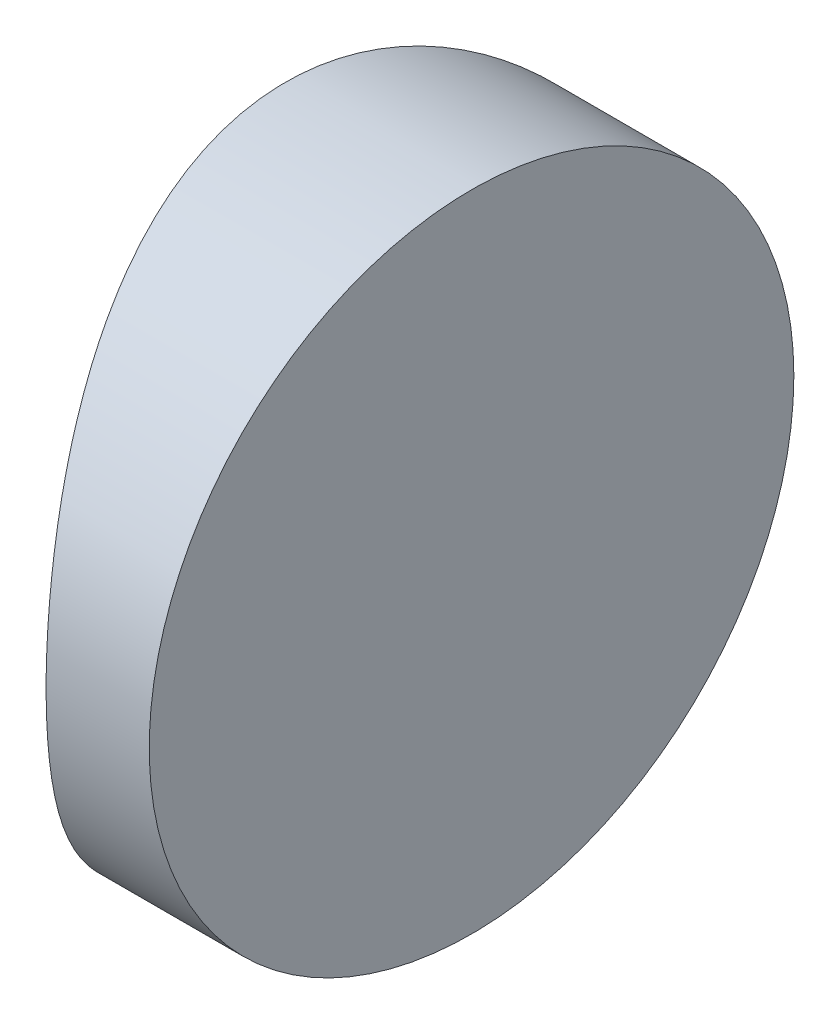
SolidWorks part; units mm, degrees
ref_plane "前视基准面" through (0, 0, 0) normal (0, 0, 1) x (1, 0, 0)
ref_plane "上视基准面" through (0, 0, 0) normal (0, 1, 0) x (1, 0, 0)
ref_plane "右视基准面" through (0, 0, 0) normal (1, 0, 0) x (0, 0, -1)
sketch "草图1" plane through (0, 0, 0) normal (0, 1, 0) x (1, 0, 0)
  line L0 (10.7432, 0) -> (-19.1624, 0) construction
  line L1 (-6.9639, 6.25) -> (-4.9648, 6.25)
  line L2 (-6.9639, -6.25) -> (-4.9648, -6.25)
  line L3 (-4.9648, 6.25) -> (-4.9648, -6.25)
  arc A0 (-6.9639, 6.25) -> (-6.9639, -6.25) centre (4.3552, 0) ccw
  point P19 (-8.5748, 0)
  point P20 (-4.9648, 0)
  dimension "D2" = 6.25
  dimension "D3" = 12.93
  dimension "D4" = 3.61
  dimension "D1" = 6.25
extrude "凸台-拉伸1" add sketch "草图1" along normal blind 12.5 contours A0 L2 L3 L1
sketch "草图2" plane through (-4.9648, 0, 0) normal (1, 0, 0) x (0, 0, -1)
  line L0 (6.25, 0) -> (-6.25, 0) construction
  line L7 (-6.25, 0) -> (6.25, 0)
  line L8 (6.25, 0) -> (6.25, 12.5)
  line L9 (6.25, 12.5) -> (-6.25, 12.5)
  line L10 (-6.25, 12.5) -> (-6.25, 0)
  line L11 (-6.25, 0) -> (6.25, 0)
  line L12 (6.25, 0) -> (6.25, 12.5)
  line L13 (6.25, 12.5) -> (-6.25, 12.5)
  line L14 (-6.25, 12.5) -> (-6.25, 0)
  circle A0 centre (0, 6.25) radius 6.25
  line M1 (-6.25, 0) -> (6.25, 0)
  line M2 (6.25, 0) -> (6.25, 12.5)
  line M3 (6.25, 12.5) -> (-6.25, 12.5)
  line M4 (-6.25, 12.5) -> (-6.25, 0)
  dimension "D1" = 12.5
  dimension "D2" = 6.25
  dimension "D3" = 0
extrude "切除-拉伸8" cut sketch "草图2" against normal blind 12.7 contours A0 L13 M4 | A0 L12 M3 | A0 L11 M2 | A0 L14 M1
